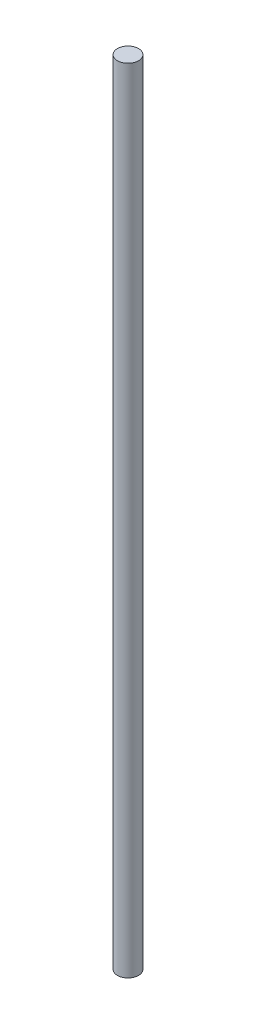
SolidWorks part; units mm, degrees
ref_plane "Front Plane" through (0, 0, 0) normal (0, 0, 1) x (1, 0, 0)
ref_plane "Top Plane" through (0, 0, 0) normal (0, 1, 0) x (1, 0, 0)
ref_plane "Right Plane" through (0, 0, 0) normal (1, 0, 0) x (0, 0, -1)
sketch "Sketch1" plane through (0, 0, 0) normal (0, 1, 0) x (1, 0, 0)
  circle A0 centre (0, 0) radius 4
  dimension "D1" = 8
extrude "Boss-Extrude1" add sketch "Sketch1" along normal blind 300
